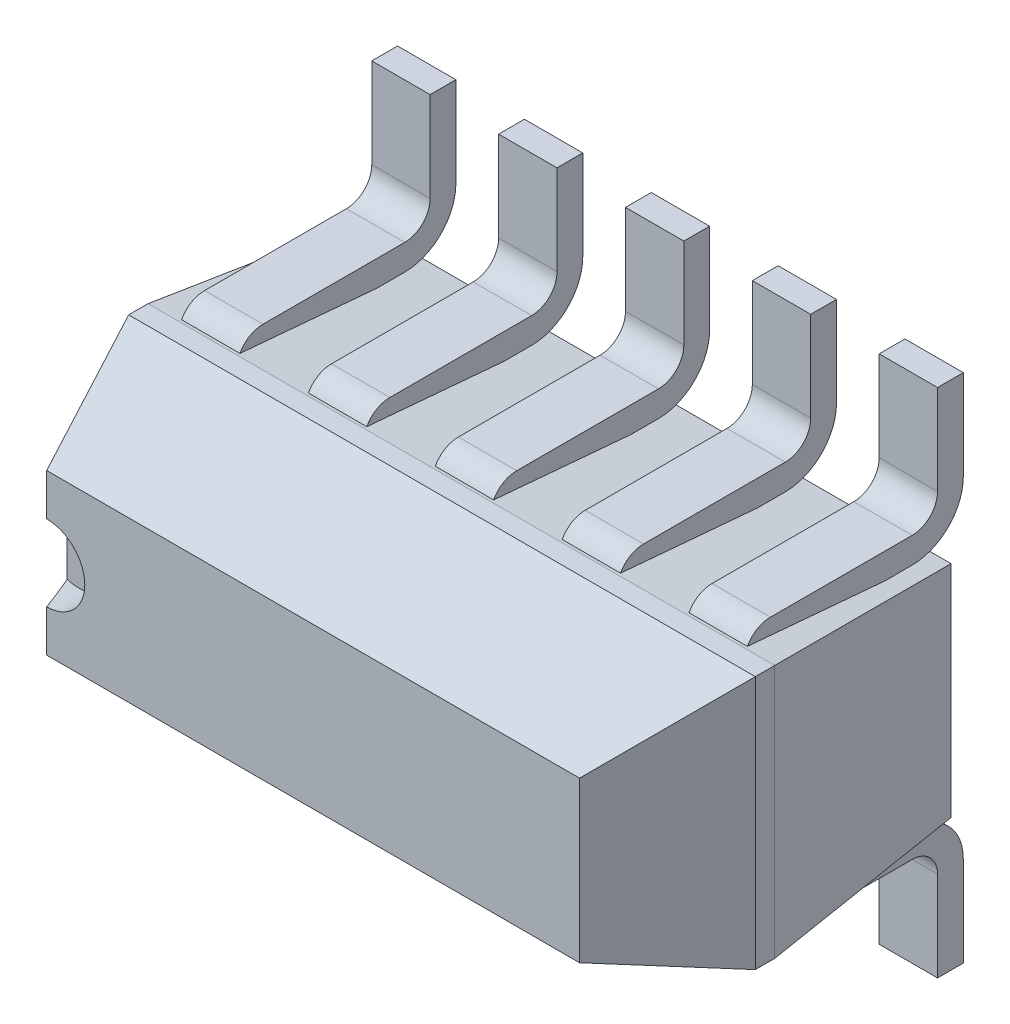
SolidWorks part; units mm, degrees
ref_plane "x/y" through (0, 0, 0) normal (0, 0, 1) x (1, 0, 0)
ref_plane "x/z" through (0, 0, 0) normal (0, 1, 0) x (1, 0, 0)
ref_plane "y/z" through (0, 0, 0) normal (1, 0, 0) x (0, 0, -1)
sketch "Sketch1" plane through (0, 0, 0) normal (0, 0, 1) x (1, 0, 0)
  line L0 (1.8805, 1.762) -> (4.3505, 1.762)
  line L1 (1.8805, 1.762) -> (1.8805, 0.762)
  line L2 (4.3505, 0.762) -> (1.8805, 0.762)
  line L3 (4.3505, 0.762) -> (4.3505, 1.762)
  dimension "D1" = 1
  dimension "D2" = 2.47
extrude "Base-Extrude" add sketch "Sketch1" along normal blind 1.3462
ref_plane "Plane1" through (1.8805, 0, 0) normal (1, 0, 0) x (0, 0, -1)
ref_plane "Plane2" through (0, 1.762, 0) normal (0, 1, 0) x (-1, 0, 0)
ref_plane "Plane3" through (4.3505, 0, 0) normal (1, 0, 0) x (0, 0, -1)
ref_plane "Plane4" through (0, 0.762, 0) normal (0, 1, 0) x (-1, 0, 0)
chamfer "Chamfer1" distance 0.508 angle 20 4 edges at (1.8805, 1.262, 1.3462) (3.1155, 1.762, 1.3462) (4.3505, 1.262, 1.3462) (3.1155, 0.762, 1.3462)
chamfer "Chamfer2" distance 0.762 angle 5 4 edges at (3.1155, 0.762, 0) (4.3505, 1.262, 0) (3.1155, 1.762, 0) (1.8805, 1.262, 0)
sketch "Sketch3" plane through (0.1189, 0.143, 1.3462) normal (0, 0, 1) x (1, 0, 0)
  line L0 (4.0467, 0.8039) -> (4.0467, 1.4341) construction
  circle A0 centre (1.9467, 1.119) radius 0.15
  dimension "D2" = 0.3
  dimension "D1" = 2.1
extrude "Cut-Extrude1" cut sketch "Sketch3" against normal blind 0.127
ref_plane "Plane5" through (2.1155, 0, 0) normal (1, 0, 0) x (0, 0, -1)
sketch "Sketch4" plane through (2.1155, 0, 0) normal (1, 0, 0) x (0, 0, -1)
  line L0 (-0.762, 0.812) -> (-0.762, 1.062)
  line L1 (0, 0.6088) -> (0, 0.2543)
  line L2 (-0.6588, 0.7088) -> (-0.1, 0.7088)
  line L4 (-1.3462, 1.412) -> (-1.3462, 1.112) construction
  line L5 (-0.762, 1.762) -> (-0.762, 0.762) construction
  arc A0 (-0.762, 0.812) -> (-0.6588, 0.7088) centre (-0.6588, 0.812) ccw
  arc A1 (-0.1, 0.7088) -> (0, 0.6088) centre (-0.1, 0.6088) cw
  point P9 (-1.3462, 1.262)
  dimension "D1" = 0.1
  dimension "D2" = 0.1
  dimension "D3" = 0.45
extrude "Boss-Extrude-Thin3" add sketch "Sketch4" along normal mid plane 0.23 thin
pattern_linear "LPattern1" count 5 spacing 0.5 along (1, 0, 0) of "Boss-Extrude-Thin3"
ref_plane "Plane6" through (0, 1.262, 0) normal (0, 1, 0) x (-1, 0, 0)
mirror "Mirror1" about plane through (0, 1.262, 0) normal (0, 1, 0) of "Boss-Extrude-Thin3", "LPattern1"
